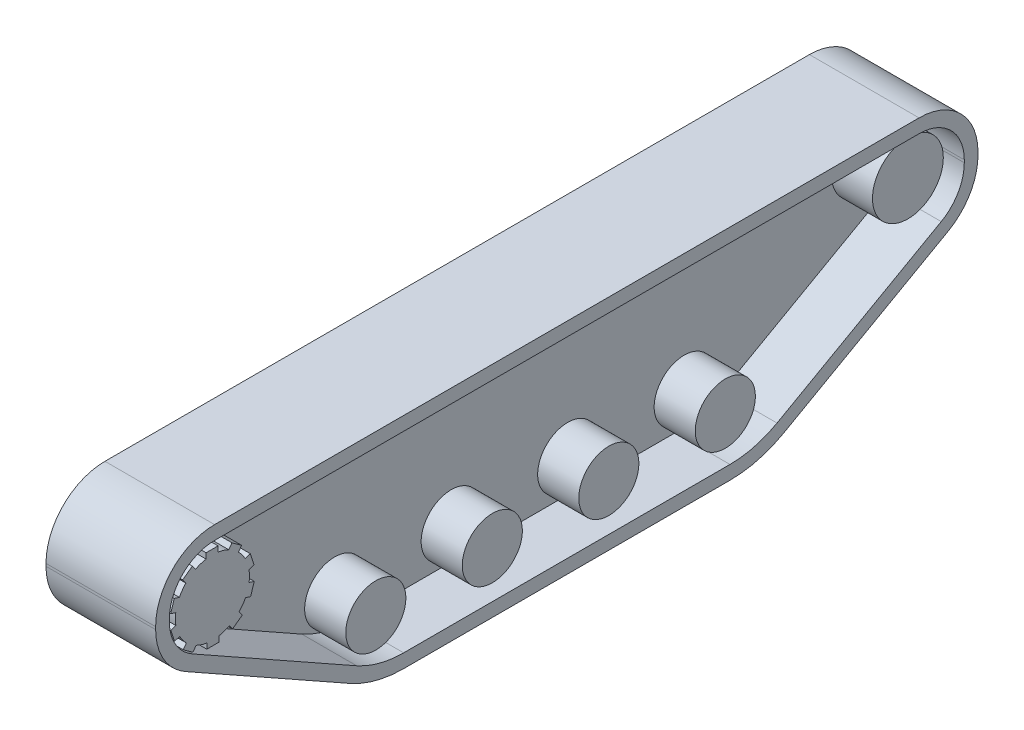
SolidWorks part; units mm, degrees
ref_plane "前视基准面" through (0, 0, 0) normal (0, 0, 1) x (1, 0, 0)
ref_plane "上视基准面" through (0, 0, 0) normal (0, 1, 0) x (1, 0, 0)
ref_plane "右视基准面" through (0, 0, 0) normal (1, 0, 0) x (0, 0, -1)
sketch "草图2" plane through (0, 0, 0) normal (1, 0, 0) x (0, 0, -1)
  line L5 (278.0812, -38.4035) -> (158.2648, -105.8003)
  line L6 (-257, 43.9258) -> (257, 43.9258)
  line L9 (-119.0439, -116.0742) -> (119.0439, -116.0742)
  line L10 (300, 0.9258) -> (300, -0.9258)
  line L11 (0, -116.0742) -> (0, 43.9258) construction
  line L12 (-300, 0) -> (300, 0) construction
  line L14 (-300, 0.9258) -> (-300, -0.9258)
  line L15 (-278.0812, -38.4035) -> (-158.2648, -105.8003)
  arc A0 (300, 0.9258) -> (257, 43.9258) centre (257, 0.9258) ccw
  arc A2 (119.0439, -116.0742) -> (158.2648, -105.8003) centre (119.0439, -36.0742) ccw
  arc A4 (278.0812, -38.4035) -> (300, -0.9258) centre (257, -0.9258) ccw
  arc A5 (-278.0812, -38.4035) -> (-300, -0.9258) centre (-257, -0.9258) cw
  arc A6 (-119.0439, -116.0742) -> (-158.2648, -105.8003) centre (-119.0439, -36.0742) cw
  arc A7 (-300, 0.9258) -> (-257, 43.9258) centre (-257, 0.9258) cw
  point P0 (0, 0)
  point P6 (0, 0)
  point P9 (300, 43.9258)
  point P13 (-300, 43.9258)
  point P16 (140, -116.0742)
  point P21 (300, -26.0742)
  point P25 (-300, -26.0742)
  point P26 (-140, -116.0742)
  dimension "D5" = 43
  dimension "D7" = 80
  dimension "D9" = 43
  dimension "D1" = 160
  dimension "D2" = 70
  dimension "D3" = 160
  dimension "D4" = 600
extrude "凸台-拉伸1" add sketch "草图2" along normal blind 80
sketch "草图3" plane through (80, 0, 0) normal (1, 0, 0) x (0, 0, -1)
  line L12 (257, 33.9258) -> (-257, 33.9258)
  line L13 (-290, 0.9258) -> (-290, -0.9258)
  line L14 (-273.1786, -29.6878) -> (-153.3622, -97.0845)
  line L15 (-119.0439, -106.0742) -> (119.0439, -106.0742)
  line L16 (153.3622, -97.0845) -> (273.1786, -29.6878)
  line L17 (290, -0.9258) -> (290, 0.9258)
  line L18 (257, 33.9258) -> (-257, 33.9258)
  line L19 (-290, 0.9258) -> (-290, -0.9258)
  line L20 (-273.1786, -29.6878) -> (-153.3622, -97.0845)
  line L21 (-119.0439, -106.0742) -> (119.0439, -106.0742)
  line L22 (153.3622, -97.0845) -> (273.1786, -29.6878)
  line L23 (290, -0.9258) -> (290, 0.9258)
  arc A12 (290, 0.9258) -> (257, 33.9258) centre (257, 0.9258) ccw
  arc A13 (-257, 33.9258) -> (-290, 0.9258) centre (-257, 0.9258) ccw
  arc A14 (-290, -0.9258) -> (-273.1786, -29.6878) centre (-257, -0.9258) ccw
  arc A15 (-153.3622, -97.0845) -> (-119.0439, -106.0742) centre (-119.0439, -36.0742) ccw
  arc A16 (119.0439, -106.0742) -> (153.3622, -97.0845) centre (119.0439, -36.0742) ccw
  arc A17 (273.1786, -29.6878) -> (290, -0.9258) centre (257, -0.9258) ccw
  arc A18 (290, 0.9258) -> (257, 33.9258) centre (257, 0.9258) ccw
  arc A19 (-257, 33.9258) -> (-290, 0.9258) centre (-257, 0.9258) ccw
  arc A20 (-290, -0.9258) -> (-273.1786, -29.6878) centre (-257, -0.9258) ccw
  arc A21 (-153.3622, -97.0845) -> (-119.0439, -106.0742) centre (-119.0439, -36.0742) ccw
  arc A22 (119.0439, -106.0742) -> (153.3622, -97.0845) centre (119.0439, -36.0742) ccw
  arc A23 (273.1786, -29.6878) -> (290, -0.9258) centre (257, -0.9258) ccw
  dimension "D1" = 10
extrude "切除-拉伸1" cut sketch "草图3" against normal blind 40
sketch "草图4" plane through (40, 0, 0) normal (1, 0, 0) x (0, 0, -1)
  line L0 (-237.2648, 20.9741) -> (-239.5468, 17.8332)
  line L1 (-263.2062, 29.2313) -> (-254.4612, 29.2313)
  line L2 (-263.2062, 29.2313) -> (-263.2062, 25.2623)
  line L4 (-254.4612, 29.2313) -> (-254.4612, 25.3489)
  line L5 (-244.3397, 26.1143) -> (-237.2648, 20.9741)
  line L6 (-244.3397, 26.1143) -> (-246.6726, 22.9034)
  line L7 (-228.2061, 4.1862) -> (-231.8984, 2.9865)
  line L8 (-230.9084, 12.5032) -> (-228.2061, 4.1862)
  line L9 (-230.9084, 12.5032) -> (-234.6832, 11.2767)
  line L10 (-230.7451, -14.7201) -> (-234.4374, -13.5204)
  line L11 (-228.0427, -6.4031) -> (-230.7451, -14.7201)
  line L12 (-228.0427, -6.4031) -> (-231.8175, -5.1766)
  line L13 (-243.9121, -28.5232) -> (-246.1941, -25.3824)
  line L14 (-236.8372, -23.383) -> (-243.9121, -28.5232)
  line L15 (-236.8372, -23.383) -> (-239.1701, -20.172)
  line L16 (-262.6777, -31.9508) -> (-262.6777, -28.0685)
  line L17 (-253.9326, -31.9508) -> (-262.6777, -31.9508)
  line L18 (-253.9326, -31.9508) -> (-253.9326, -27.9818)
  line L19 (-279.874, -23.6937) -> (-277.592, -20.5528)
  line L20 (-272.7991, -28.8339) -> (-279.874, -23.6937)
  line L21 (-272.7991, -28.8339) -> (-270.4662, -25.6229)
  line L22 (-288.9327, -6.9058) -> (-285.2404, -5.7061)
  line L23 (-286.2304, -15.2228) -> (-288.9327, -6.9058)
  line L24 (-286.2304, -15.2228) -> (-282.4556, -13.9963)
  line L25 (-286.3937, 12.0005) -> (-282.7014, 10.8008)
  line L26 (-289.0961, 3.6835) -> (-286.3937, 12.0005)
  line L27 (-289.0961, 3.6835) -> (-285.3213, 2.457)
  line L28 (-273.2267, 25.8037) -> (-270.9448, 22.6628)
  line L29 (-280.3016, 20.6634) -> (-273.2267, 25.8037)
  line L30 (-280.3016, 20.6634) -> (-277.9687, 17.4524)
  arc A0 (-285.3213, 2.457) -> (-285.2404, -5.7061) centre (-258.5694, -1.3598) ccw
  arc A1 (-277.9687, 17.4524) -> (-282.7014, 10.8008) centre (-258.5694, -1.3598) ccw
  arc A2 (-263.2062, 25.2623) -> (-270.9448, 22.6628) centre (-258.5694, -1.3598) ccw
  arc A3 (-246.6726, 22.9034) -> (-254.4612, 25.3489) centre (-258.5694, -1.3598) ccw
  arc A4 (-234.6832, 11.2767) -> (-239.5468, 17.8332) centre (-258.5694, -1.3598) ccw
  arc A5 (-231.8175, -5.1766) -> (-231.8984, 2.9865) centre (-258.5694, -1.3598) ccw
  arc A6 (-239.1701, -20.172) -> (-234.4374, -13.5204) centre (-258.5694, -1.3598) ccw
  arc A7 (-253.9326, -27.9818) -> (-246.1941, -25.3824) centre (-258.5694, -1.3598) ccw
  arc A8 (-270.4662, -25.6229) -> (-262.6777, -28.0685) centre (-258.5694, -1.3598) ccw
  arc A9 (-282.4556, -13.9963) -> (-277.592, -20.5528) centre (-258.5694, -1.3598) ccw
  point P45 (-258.5694, -1.3598)
  dimension "D1" = 10
extrude "凸台-拉伸2" add sketch "草图4" along normal blind 40
sketch "草图5" plane through (40, 0, 0) normal (1, 0, 0) x (0, 0, -1)
  circle A0 centre (-129.3541, -82.2458) radius 21.9308
  circle A1 centre (-44.3541, -82.2458) radius 21.9308
  circle A2 centre (40.6459, -82.2458) radius 21.9308
  circle A3 centre (125.6459, -82.2458) radius 21.9308
  circle A4 centre (258.8477, 0) radius 25.8475
  dimension "D1" = 4
extrude "凸台-拉伸3" add sketch "草图5" along normal blind 30
sketch "草图6" plane through (0, 0, 0) normal (-1, 0, 0) x (0, 0, 1)
  line L0 (0, 169.4048) -> (0, -68.573) construction
  line L1 (-257, 43.9258) -> (257, 43.9258) construction
  circle A0 centre (-180, -16.0742) radius 10
  circle A2 centre (180, -16.0742) radius 10
  dimension "D1" = 20
  dimension "D2" = 60
  dimension "D3" = 180
extrude "凸台-拉伸4" add sketch "草图6" along normal blind 20
